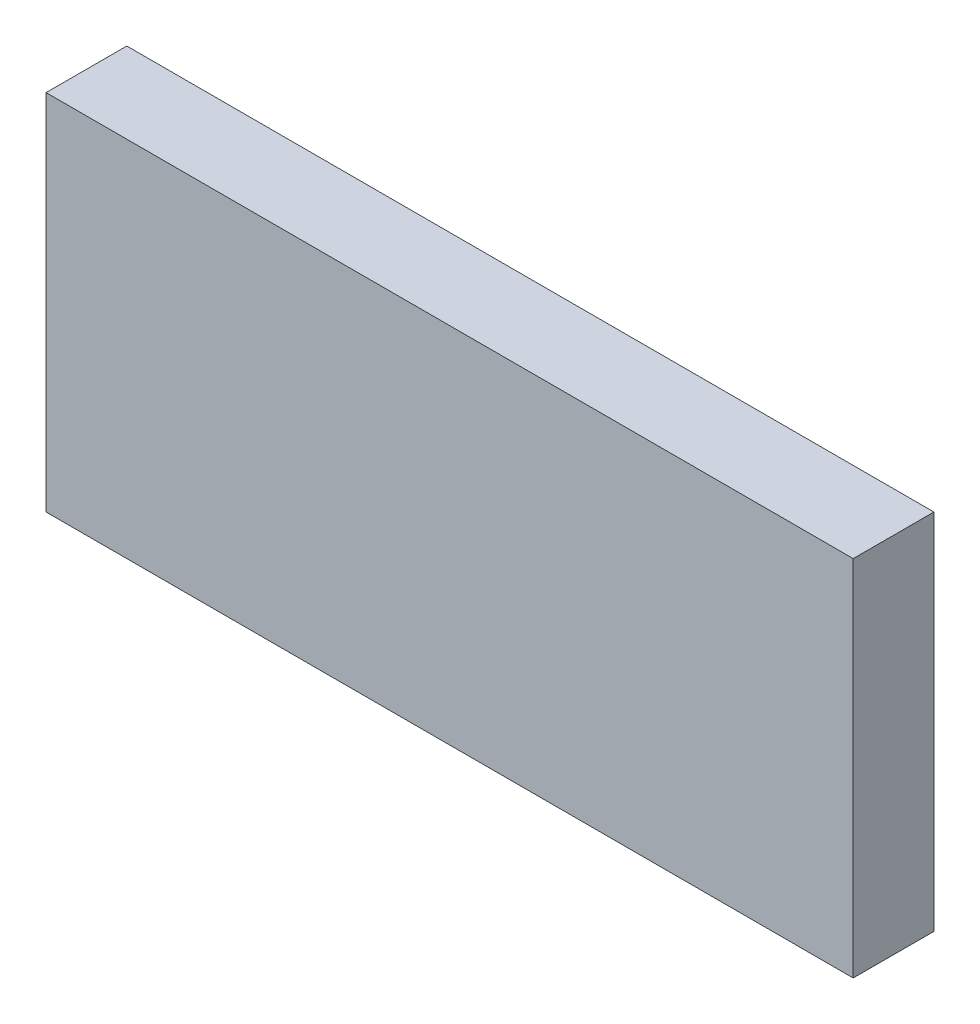
SolidWorks part; units mm, degrees
ref_plane "Front Plane" through (0, 0, 0) normal (0, 0, 1) x (1, 0, 0)
ref_plane "Top Plane" through (0, 0, 0) normal (0, 1, 0) x (1, 0, 0)
ref_plane "Right Plane" through (0, 0, 0) normal (1, 0, 0) x (0, 0, -1)
sketch "Sketch3" plane through (0, 0, 0) normal (0, 0, 1) x (1, 0, 0)
  line L1 (-59.707, 29.4409) -> (-19.707, 29.4409)
  line L2 (-59.707, 29.4409) -> (-59.707, 11.4409)
  line L3 (-59.707, 11.4409) -> (-19.707, 11.4409)
  line L4 (-19.707, 29.4409) -> (-19.707, 11.4409)
extrude "Boss-Extrude1" add sketch "Sketch3" along normal blind 4 contours L1 L4 L3 L2
